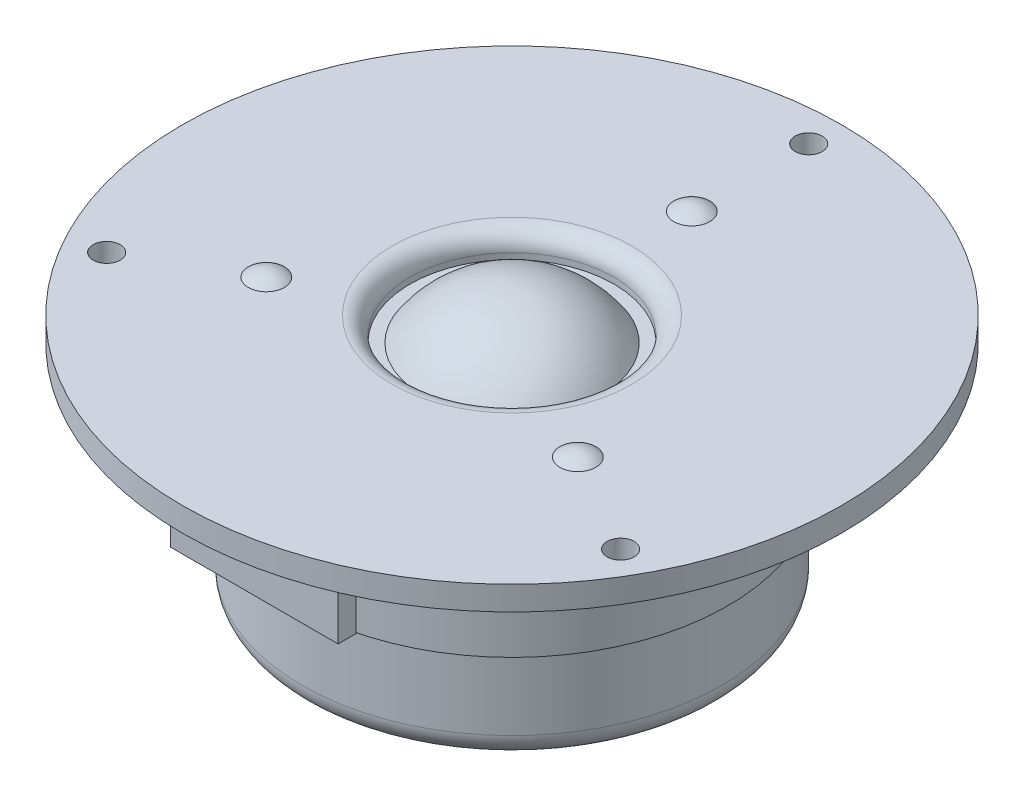
SolidWorks part; units mm, degrees
ref_plane "Front Plane" through (0, 0, 0) normal (0, 0, 1) x (1, 0, 0)
ref_plane "Top Plane" through (0, 0, 0) normal (0, 1, 0) x (1, 0, 0)
ref_plane "Right Plane" through (0, 0, 0) normal (1, 0, 0) x (0, 0, -1)
sketch "Sketch2" plane through (0, 0, 0) normal (0, 0, 1) x (1, 0, 0)
  line L0 (0, 0) -> (0, 18.6932) construction
  line L1 (0, 8.0501) -> (0, -36)
  line L2 (0, -36) -> (35, -36)
  line L3 (35, -36) -> (35, -20)
  line L4 (35, -20) -> (36, -20)
  line L5 (36, -20) -> (36, -8)
  line L6 (36, -8) -> (35, -8)
  line L7 (35, -8) -> (35, -4)
  line L8 (35, -4) -> (37, -4)
  line L9 (37, -4) -> (37, 0)
  line L10 (37, 0) -> (55, 0)
  line L11 (55, 0) -> (55, 4)
  line L13 (55, 4) -> (17, 4)
  line L14 (17, 4) -> (17, 0)
  line L15 (17, 0) -> (15, 0)
  arc A0 (15, 0) -> (0, 8.0501) centre (0, -9.9499) ccw
  point P3 (0, 0)
  point P19 (15.4705, 1)
  dimension "D3" = 18
  dimension "D4" = 30
  dimension "D1" = 110
  dimension "D2" = 4
  dimension "D5" = 74
  dimension "D6" = 4
  dimension "D7" = 4
  dimension "D8" = 12
  dimension "D9" = 1
  dimension "D10" = 4
  dimension "D11" = 70
  dimension "D12" = 34
revolve "Revolve1" add sketch "Sketch2" angle 360 about L0
fillet "Fillet1" radius 4 1 edges at (0, -36, -35)
fillet "Fillet2" radius 3 1 edges at (0, 4, -17)
hole_wizard "M4 Clearance Hole1" positions "Sketch3" profile "Sketch4" hole size "M4" standard "ANSI Metric"
sketch "Sketch3" plane through (0, 4, 0) normal (0, 1, 0) x (1, 0, 0)
  point P0 (0, 49.5)
  dimension "D1" = 49.5
sketch "Sketch4" plane through (0, 4, -49.5) normal (1, 0, 0) x (0, 0, 1)
  line L0 (0, 0) -> (0, 12)
  line L1 (0, 12) -> (2.25, 12)
  line L2 (2.25, 12) -> (2.25, 0)
  line L5 (2.25, 0) -> (0, 0)
  line L10 (0, 12) -> (-2.25, 12) construction
  line L11 (0, -6.35) -> (0, 107.95) construction
  dimension "Hole Dia." = 4.5
  dimension "Hole Depth" = 12
  dimension "Drill Angle" = 180
sketch "Sketch6" plane through (0, 0, 0) normal (1, 0, 0) x (0, 0, -1)
  line L0 (33, 4) -> (30, 4)
  line L1 (30, 5) -> (30, 4)
  line L2 (55, 4) -> (-55, 4) construction
  line L3 (30, 5) -> (30, 0) construction
  arc A0 (33, 4) -> (30, 5) centre (30, 0) ccw
  point P3 (30, 5)
  dimension "D1" = 6
  dimension "D2" = 1
  dimension "D3" = 30
revolve "Revolve3" add sketch "Sketch6" angle 360 about L3
pattern_circular "CirPattern1" count 3 over 360 about axis through (0, 0, 0) along (0, 1, 0) of "M4 Clearance Hole1", "Revolve3"
sketch "Sketch7" plane through (0, 0, 0) normal (0, -1, 0) x (1, 0, 0)
  line L0 (0, 40) -> (0, 0) construction
  line L1 (-14, 43) -> (14, 43)
  line L2 (-14, 43) -> (-14, 40)
  line L3 (-14, 40) -> (14, 40)
  line L4 (14, 43) -> (14, 40)
  dimension "D1" = 28
  dimension "D2" = 3
  dimension "D3" = 40
extrude "Boss-Extrude1" add sketch "Sketch7" along normal blind 15
